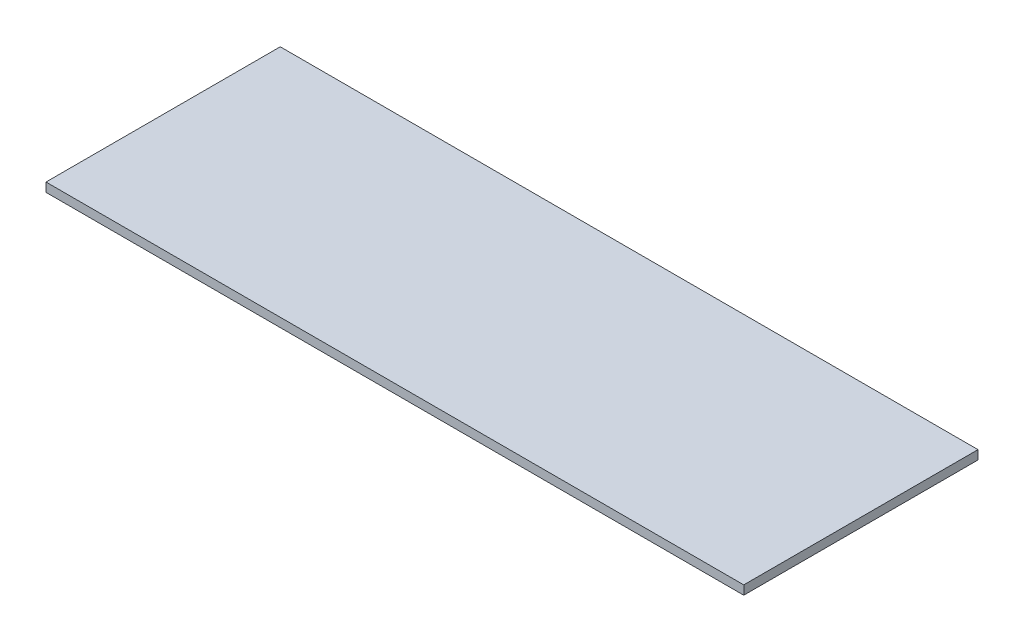
SolidWorks part; units mm, degrees
ref_plane "Front Plane" through (0, 0, 0) normal (0, 0, 1) x (1, 0, 0)
ref_plane "Top Plane" through (0, 0, 0) normal (0, 1, 0) x (1, 0, 0)
ref_plane "Right Plane" through (0, 0, 0) normal (1, 0, 0) x (0, 0, -1)
sketch "Sketch1" plane through (0, 0, 0) normal (0, 1, 0) x (1, 0, 0)
  line L1 (0, 0) -> (1400, 0)
  line L2 (0, 0) -> (0, 470)
  line L3 (0, 470) -> (1400, 470)
  line L4 (1400, 0) -> (1400, 470)
  dimension "D1" = 470
  dimension "D2" = 1400
extrude "Boss-Extrude1" add sketch "Sketch1" along normal blind 18
